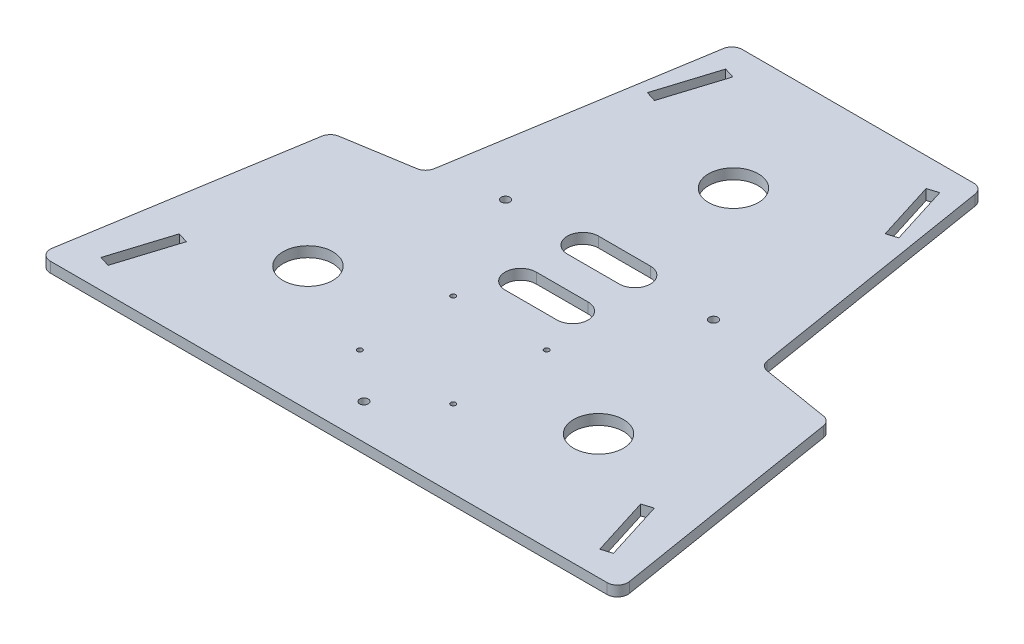
SolidWorks part; units mm, degrees
material "Acrylic (Medium-high impact)"
ref_plane "Front Plane" through (0, 0, 0) normal (0, 0, 1) x (1, 0, 0)
ref_plane "Top Plane" through (0, 0, 0) normal (0, 1, 0) x (1, 0, 0)
ref_plane "Right Plane" through (0, 0, 0) normal (1, 0, 0) x (0, 0, -1)
sketch "Sketch1" plane through (0, 0, 0) normal (0, 1, 0) x (1, 0, 0)
  line L0 (-134.1189, 0) -> (134.1189, 0)
  line L1 (139.0537, 5.8045) -> (120.843, 117.5127)
  line L2 (116.7126, 121.6431) -> (84.3366, 126.921)
  line L3 (80.2062, 131.0514) -> (60.684, 250.8045)
  line L4 (-55.7491, 255) -> (55.7491, 255)
  line L5 (12.5, 135) -> (-12.5, 135) construction
  line L6 (-60.684, 250.8045) -> (-80.2062, 131.0514)
  line L7 (-84.3366, 126.921) -> (-116.7126, 121.6431)
  line L8 (-120.843, 117.5127) -> (-139.0537, 5.8045)
  line L9 (0, 0) -> (0, 255) construction
  line L10 (12.5, 127.5) -> (-12.5, 127.5)
  line L11 (12.5, 142.5) -> (-12.5, 142.5)
  line L12 (12.5, 105) -> (-12.5, 105) construction
  line L13 (12.5, 97.5) -> (-12.5, 97.5)
  line L14 (12.5, 112.5) -> (-12.5, 112.5)
  line L15 (-70, 60) -> (0, 195) construction
  line L16 (0, 195) -> (70, 60) construction
  line L17 (70, 60) -> (-70, 60) construction
  line L18 (-50.0918, 135.3254) -> (-35, 127.5) construction
  circle A0 centre (0, 195) radius 12
  circle A1 centre (-70, 60) radius 12
  circle A2 centre (70, 60) radius 12
  arc A3 (60.684, 250.8045) -> (55.7491, 255) centre (55.7491, 250) ccw
  arc A4 (84.3366, 126.921) -> (80.2062, 131.0514) centre (85.1411, 131.8559) cw
  arc A5 (120.843, 117.5127) -> (116.7126, 121.6431) centre (115.9081, 116.7082) ccw
  arc A6 (134.1189, 0) -> (139.0537, 5.8045) centre (134.1189, 5) ccw
  arc A7 (-139.0537, 5.8045) -> (-134.1189, 0) centre (-134.1189, 5) ccw
  arc A8 (-116.7126, 121.6431) -> (-120.843, 117.5127) centre (-115.9081, 116.7082) ccw
  arc A9 (-80.2062, 131.0514) -> (-84.3366, 126.921) centre (-85.1411, 131.8559) cw
  arc A10 (-55.7491, 255) -> (-60.684, 250.8045) centre (-55.7491, 250) ccw
  arc A11 (12.5, 127.5) -> (12.5, 142.5) centre (12.5, 135) ccw
  arc A12 (-12.5, 142.5) -> (-12.5, 127.5) centre (-12.5, 135) ccw
  arc A13 (12.5, 97.5) -> (12.5, 112.5) centre (12.5, 105) ccw
  arc A14 (-12.5, 112.5) -> (-12.5, 97.5) centre (-12.5, 105) ccw
  circle A15 centre (-22.5, 82.5) radius 1.2
  circle A16 centre (22.5, 82.5) radius 1.2
  circle A17 centre (22.5, 37.5) radius 1.2
  circle A18 centre (-22.5, 37.5) radius 1.2
  circle A19 centre (-50.0918, 135.3254) radius 2.075
  circle A20 centre (50.0918, 135.3254) radius 2.075
  circle A21 centre (0, 17) radius 2.075
  point P19 (60, 255)
  point P22 (80.7852, 127.5)
  point P25 (120.264, 121.0641)
  point P28 (140, 0)
  point P31 (-140, 0)
  point P34 (-120.264, 121.0641)
  point P37 (-80.7852, 127.5)
  point P40 (-60, 255)
  point P43 (0, 135)
  point P50 (0, 105)
  dimension "D1" = 24
  dimension "D2" = 24
  dimension "D3" = 24
  dimension "D12" = 5
  dimension "D13" = 7.5
  dimension "D17" = 2.4
  dimension "D21" = 4.15
  dimension "D4" = 60
  dimension "D5" = 60
  dimension "D6" = 140
  dimension "D7" = 135
  dimension "D8" = 127.5
  dimension "D9" = 280
  dimension "D10" = 120
  dimension "D11" = 40
  dimension "D14" = 25
  dimension "D15" = 30
  dimension "D16" = 105
  dimension "D18" = 45
  dimension "D19" = 45
  dimension "D20" = 37.5
  dimension "D22" = 17
  dimension "D23" = 17
extrude "Boss-Extrude1" add sketch "Sketch1" along normal blind 5
sketch "Sketch2" plane through (0, 5, 0) normal (0, 1, 0) x (1, 0, 0)
  line L0 (0, 0) -> (0, 255) construction
  line L1 (55.7491, 255) -> (-55.7491, 255) construction
  line L2 (-125, 0) -> (-45, 255) construction
  line L3 (-60.579, 214.1112) -> (-51.5689, 242.8311)
  line L4 (-134.1189, 0) -> (134.1189, 0) construction
  line L5 (-60.579, 214.1112) -> (-55.5697, 212.5397)
  line L6 (-51.5689, 242.8311) -> (-46.5596, 241.2595)
  line L7 (-55.5697, 212.5397) -> (-46.5596, 241.2595)
  line L8 (-60.579, 214.1112) -> (-46.5596, 241.2595) construction
  line L9 (-51.5689, 242.8311) -> (-55.5697, 212.5397) construction
  line L10 (109.421, 40.8888) -> (123.4404, 13.7405) construction
  line L11 (-118.4311, 12.1689) -> (-109.421, 40.8888)
  line L12 (-118.4311, 12.1689) -> (-123.4404, 13.7405)
  line L13 (-109.421, 40.8888) -> (-114.4303, 42.4603)
  line L14 (-123.4404, 13.7405) -> (-114.4303, 42.4603)
  line L15 (-118.4311, 12.1689) -> (-114.4303, 42.4603) construction
  line L16 (-109.421, 40.8888) -> (-123.4404, 13.7405) construction
  line L17 (118.4311, 12.1689) -> (114.4303, 42.4603) construction
  line L18 (51.5689, 242.8311) -> (55.5697, 212.5397) construction
  line L19 (60.579, 214.1112) -> (46.5596, 241.2595) construction
  line L20 (125, 0) -> (45, 255) construction
  line L21 (123.4404, 13.7405) -> (114.4303, 42.4603)
  line L22 (109.421, 40.8888) -> (114.4303, 42.4603)
  line L23 (118.4311, 12.1689) -> (123.4404, 13.7405)
  line L24 (118.4311, 12.1689) -> (109.421, 40.8888)
  line L25 (55.5697, 212.5397) -> (46.5596, 241.2595)
  line L26 (51.5689, 242.8311) -> (46.5596, 241.2595)
  line L27 (60.579, 214.1112) -> (55.5697, 212.5397)
  line L28 (60.579, 214.1112) -> (51.5689, 242.8311)
  line L29 (-85, 127.5) -> (-163.8083, 152.2242) construction
  point P10 (-53.5693, 227.6854)
  point P13 (-116.4307, 27.3146)
  point P31 (116.4307, 27.3146)
  point P32 (53.5693, 227.6854)
  dimension "D1" = 125
  dimension "D2" = 45
  dimension "D3" = 5.25
  dimension "D4" = 30.1
  dimension "D5" = 179.9
extrude "Cut-Extrude1" cut sketch "Sketch2" against normal blind 5
